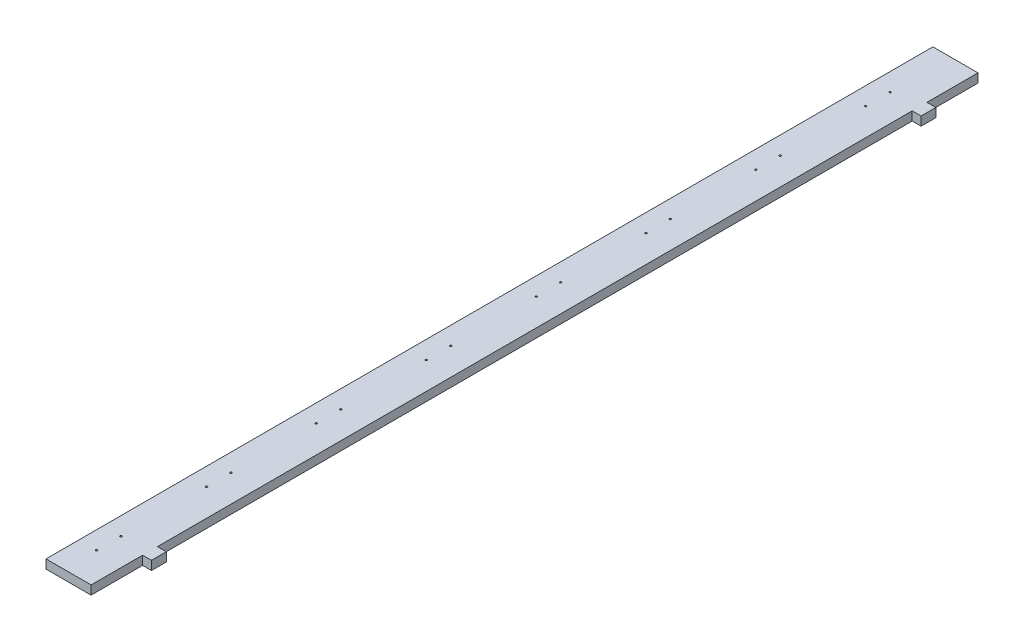
SolidWorks part; units mm, degrees
ref_plane "Front Plane" through (0, 0, 0) normal (0, 0, 1) x (1, 0, 0)
ref_plane "Top Plane" through (0, 0, 0) normal (0, 1, 0) x (1, 0, 0)
ref_plane "Right Plane" through (0, 0, 0) normal (1, 0, 0) x (0, 0, -1)
sketch "Sketch1" plane through (0, 0, 0) normal (0, 1, 0) x (1, 0, 0)
  line L1 (0, 0) -> (61, 0)
  line L2 (0, 0) -> (0, 1200)
  line L3 (0, 1200) -> (61, 1200)
  line L4 (61, 0) -> (61, 1200)
  dimension "D1" = 1200
  dimension "D2" = 61
extrude "Boss-Extrude1" add sketch "Sketch1" along normal blind 12
sketch "Sketch2" plane through (0, 12, 0) normal (0, 1, 0) x (1, 0, 0)
  circle A0 centre (24.1409, 77.395) radius 1.25
  circle A1 centre (24.1409, 44.395) radius 1.25
  circle A2 centre (24.1409, 226.045) radius 1.25
  circle A3 centre (24.1409, 193.045) radius 1.25
  circle A4 centre (24.1409, 374.695) radius 1.25
  circle A5 centre (24.1409, 341.695) radius 1.25
  circle A6 centre (24.1409, 523.345) radius 1.25
  circle A7 centre (24.1409, 490.345) radius 1.25
  circle A8 centre (24.1409, 671.995) radius 1.25
  circle A9 centre (24.1409, 638.995) radius 1.25
  circle A10 centre (24.1409, 820.645) radius 1.25
  circle A11 centre (24.1409, 787.645) radius 1.25
  circle A12 centre (24.1409, 969.295) radius 1.25
  circle A13 centre (24.1409, 936.295) radius 1.25
  circle A14 centre (24.1409, 1117.945) radius 1.25
  circle A15 centre (24.1409, 1084.945) radius 1.25
  dimension "D1" = 2.5
  dimension "D2" = 8
extrude "Cut-Extrude1" cut sketch "Sketch2" against normal blind 20
sketch "Sketch3" plane through (0, 12, 0) normal (0, 1, 0) x (1, 0, 0)
  line L0 (61, 0) -> (61, 1200) construction
  line L1 (49.5795, 69.7) -> (73, 69.7)
  line L2 (49.5795, 69.7) -> (49.5795, 89.7)
  line L3 (49.5795, 89.7) -> (73, 89.7)
  line L4 (73, 69.7) -> (73, 89.7)
  line L5 (0, 0) -> (61, 0) construction
  line L6 (49.5795, 1110.95) -> (73, 1110.95)
  line L7 (49.5795, 1110.95) -> (49.5795, 1130.95)
  line L8 (49.5795, 1130.95) -> (73, 1130.95)
  line L9 (73, 1110.95) -> (73, 1130.95)
  dimension "D1" = 12
  dimension "D2" = 20
  dimension "D3" = 69.7
  dimension "D4" = 2
extrude "Boss-Extrude2" add sketch "Sketch3" against normal blind 12
